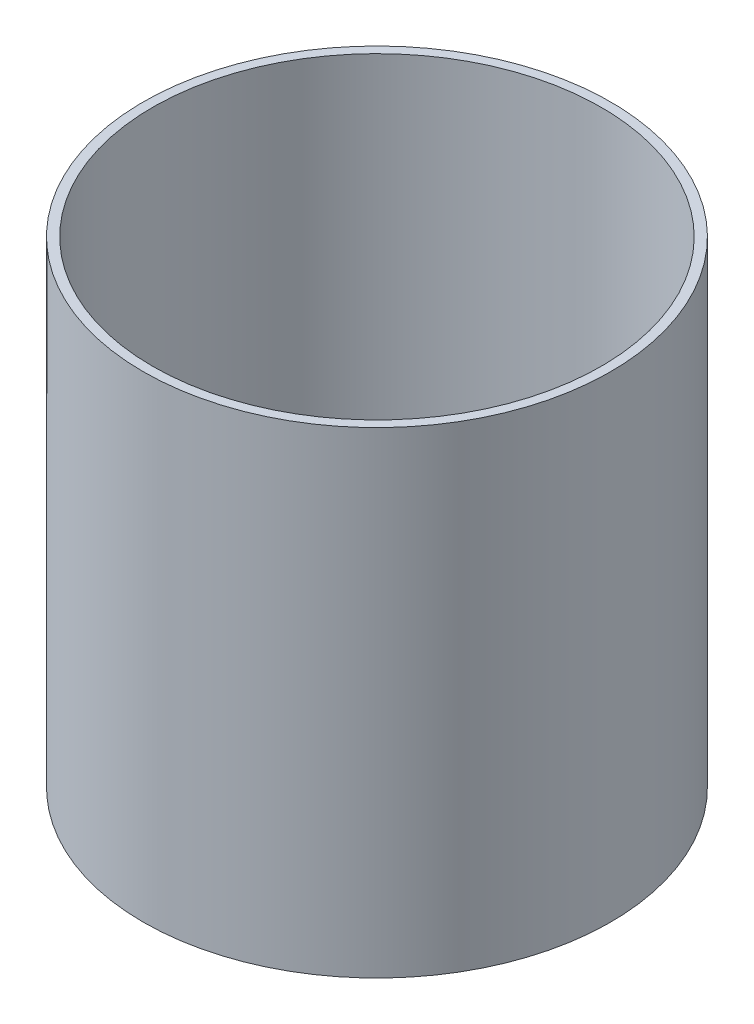
SolidWorks part; units mm, degrees
ref_plane "Front Plane" through (0, 0, 0) normal (0, 0, 1) x (1, 0, 0)
ref_plane "Top Plane" through (0, 0, 0) normal (0, 1, 0) x (1, 0, 0)
ref_plane "Right Plane" through (0, 0, 0) normal (1, 0, 0) x (0, 0, -1)
sketch "Sketch1" plane through (0, 0, 0) normal (0, 1, 0) x (1, 0, 0)
  circle A0 centre (0, 0) radius 50
  dimension "D1" = 100
extrude "Boss-Extrude1" add sketch "Sketch1" along normal blind 2
sketch "Sketch4" plane through (0, 2, 0) normal (0, 1, 0) x (1, 0, 0)
  circle A0 centre (-7.5, 0) radius 2
  circle A1 centre (7.5, 0) radius 2
  dimension "D1" = 4
  dimension "D2" = 4
  dimension "D3" = 7.5
  dimension "D4" = 7.5
extrude "Cut-Extrude1" cut sketch "Sketch4" against normal up to surface (2 mm away) up to face at (0, 0, 50)
sketch "Sketch5" plane through (0, 2, 0) normal (0, 1, 0) x (1, 0, 0)
  circle A0 centre (0, 0) radius 50
  circle A1 centre (0, 0) radius 48
  circle A2 centre (0, 0) radius 50 construction
  dimension "D1" = 2
extrude "Boss-Extrude2" add sketch "Sketch5" along normal blind 100
sketch "Sketch6" plane through (0, 2, 0) normal (0, 1, 0) x (1, 0, 0)
  circle A0 centre (0, 0) radius 2
extrude "Boss-Extrude3" add sketch "Sketch6" along normal blind 20
sketch "Sketch7" plane through (0, 2, 0) normal (0, 1, 0) x (1, 0, 0)
  circle A1 centre (0, -35) radius 3.5
  dimension "D1" = 35
extrude "Cut-Extrude2" cut sketch "Sketch7" against normal blind 5
sketch "Sketch8" plane through (0, 2, 0) normal (0, 1, 0) x (1, 0, 0)
  circle A0 centre (0.2389, -32.0083) radius 1.45 construction
  circle A1 centre (-32.7249, 0.3185) radius 1.45 construction
  circle A2 centre (-0.2389, 32.9637) radius 1.45 construction
  circle A3 centre (31.7694, 0.1592) radius 1.45 construction
  circle A4 centre (0.2389, -32.0083) radius 1.45
  circle A5 centre (-32.7249, 0.3185) radius 1.45
  circle A6 centre (-0.2389, 32.9637) radius 1.45
  circle A7 centre (31.7694, 0.1592) radius 1.45
extrude "Cut-Extrude3" cut sketch "Sketch8" against normal blind 10
